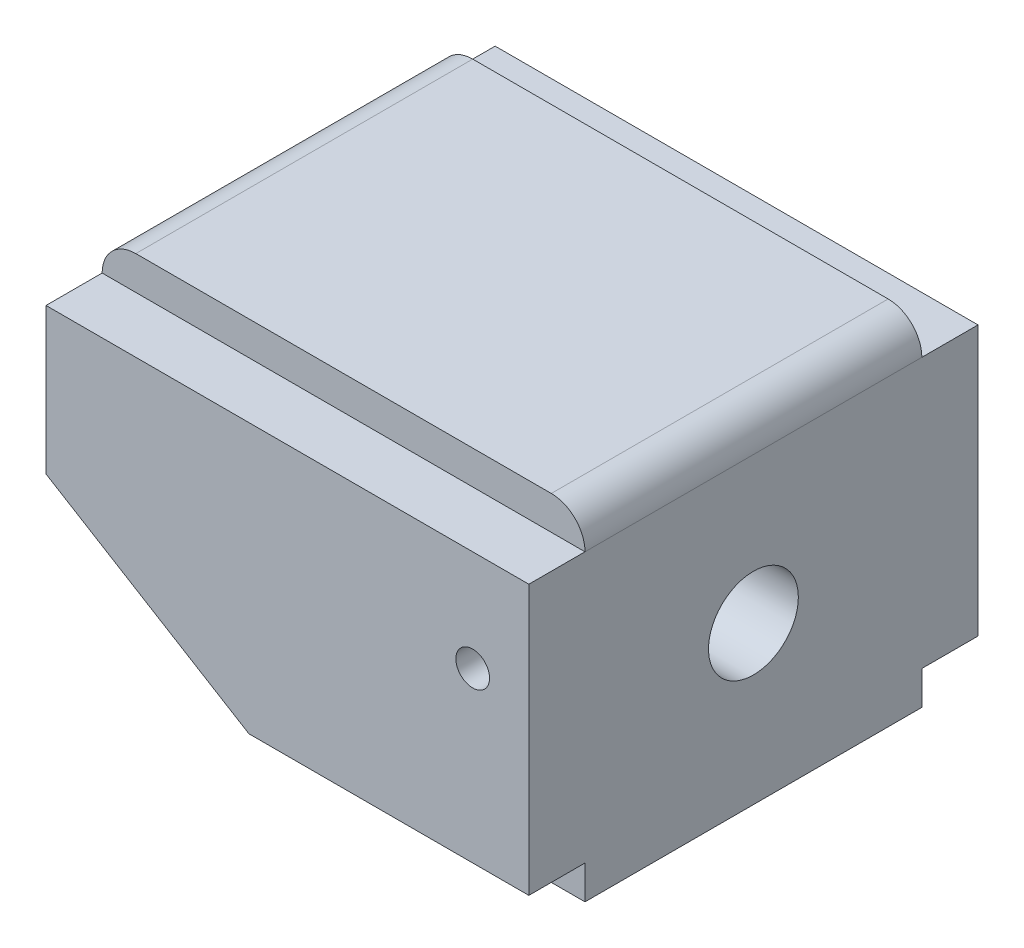
SolidWorks part; units mm, degrees
ref_plane "정면" through (0, 0, 0) normal (0, 0, 1) x (1, 0, 0)
ref_plane "윗면" through (0, 0, 0) normal (0, 1, 0) x (1, 0, 0)
ref_plane "우측면" through (0, 0, 0) normal (1, 0, 0) x (0, 0, -1)
sketch "스케치1" plane through (0, 0, 0) normal (0, 0, 1) x (1, 0, 0)
  line L0 (0, 0) -> (-20, 0)
  line L1 (-20, 0) -> (-43, 14)
  line L2 (-43, 14) -> (-43, 30)
  line L3 (-43, 30) -> (0, 30)
  line L4 (0, 30) -> (0, 0)
  dimension "D1" = 20
  dimension "D2" = 43
  dimension "D3" = 30
  dimension "D4" = 16
extrude "보스-돌출1" add sketch "스케치1" along normal mid plane 30
fillet "필렛1" radius 3 2 edges at (0, 30, 0) (-43, 30, 0)
sketch "스케치2" plane through (0, 0, 15) normal (0, 0, 1) x (1, 0, 0)
  line L0 (-43, 27) -> (0, 27)
  line L1 (0, 27) -> (0, 3)
  line L2 (0, 0) -> (0, 27) construction
  line L3 (0, 3) -> (-24.9286, 3)
  line L4 (-43, 14) -> (-20, 0) construction
  line L5 (-24.9286, 3) -> (-43, 14)
  line L6 (-43, 14) -> (-43, 27)
  line L7 (-20, 0) -> (0, 0) construction
  dimension "D1" = 3
extrude "보스-돌출2" add sketch "스케치2" along normal blind 5 and the other way blind 35
hole_wizard "M4 여유 구멍1" positions "스케치3" profile "스케치4" hole size "M4" standard "KS" end condition through all
sketch "스케치3" plane through (0, 0, 20) normal (0, 0, 1) x (1, 0, 0)
  line L1 (-3, 30) -> (-40, 30) construction
  line L2 (0, 3) -> (0, 27) construction
  point P0 (-5, 18)
  dimension "D1" = 12
  dimension "D2" = 5
sketch "스케치4" plane through (-5, 18, 20) normal (1, 0, 0) x (0, -1, 0)
  line L0 (0, 0) -> (0, 40)
  line L1 (0, 40) -> (1.5, 40)
  line L2 (1.5, 40) -> (1.5, 0)
  line L5 (1.5, 0) -> (0, 0)
  line L11 (0, -6.35) -> (0, 107.95) construction
  dimension "관통 구멍 지름" = 3
  dimension "관통 구멍 깊이" = 40
hole_wizard "M4 여유 구멍2" positions "스케치5" profile "스케치6" hole size "M4" standard "KS"
sketch "스케치5" plane through (0, 0, 0) normal (1, 0, 0) x (0, 0, -1)
  line L0 (-15, 30) -> (15, 30) construction
  point P0 (0, 14)
  dimension "D1" = 16
sketch "스케치6" plane through (0, 14, 0) normal (0, 1, 0) x (0, 0, -1)
  line L0 (0, 0) -> (0, 15.4034)
  line L1 (0, 15.4034) -> (4, 13)
  line L2 (4, 13) -> (4, 0)
  line L5 (4, 0) -> (0, 0)
  line L10 (0, 15.4034) -> (-4, 13) construction
  line L11 (0, -6.35) -> (0, 107.95) construction
  dimension "구멍 지름" = 8
  dimension "구멍 깊이" = 13
  dimension "드릴 각도" = 118
